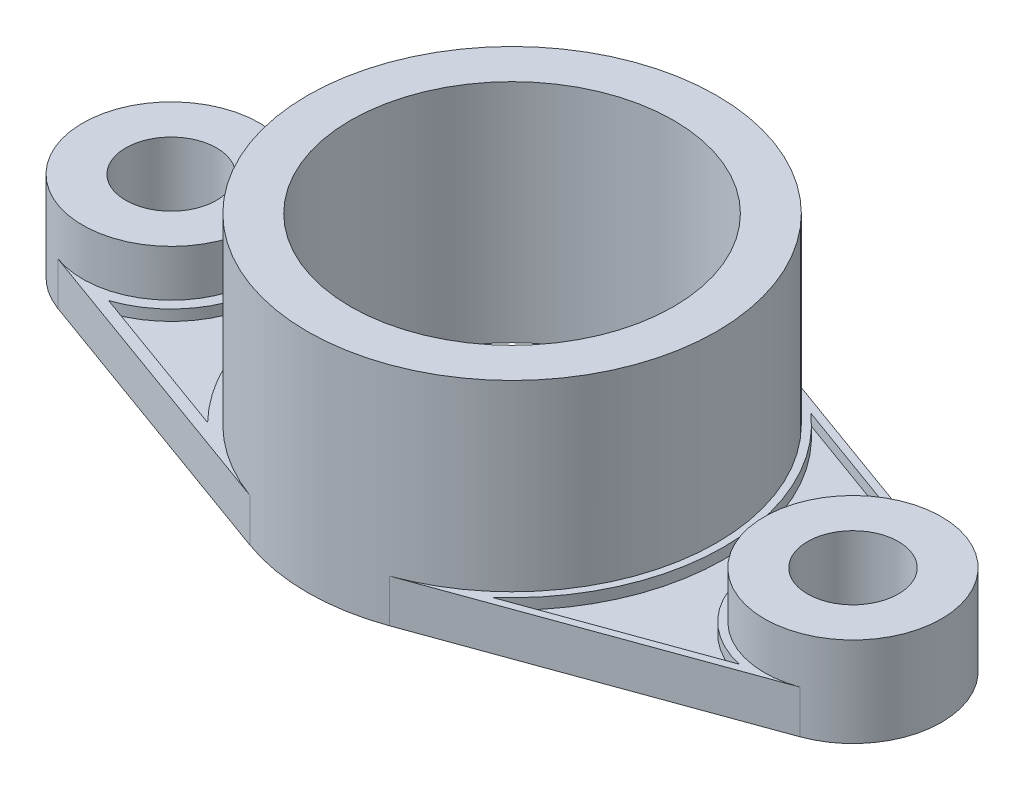
SolidWorks part; units mm, degrees
material "Polybutadiene (PB)"
ref_plane "Front Plane" through (0, 0, 0) normal (0, 0, 1) x (1, 0, 0)
ref_plane "Top Plane" through (0, 0, 0) normal (0, 1, 0) x (1, 0, 0)
ref_plane "Right Plane" through (0, 0, 0) normal (1, 0, 0) x (0, 0, -1)
sketch "Sketch1" plane through (0, 0, 0) normal (0, 1, 0) x (1, 0, 0)
  line L0 (-103.3953, 23.194) -> (-19.4, 53.597)
  line L1 (19.4, 53.597) -> (103.3953, 23.194)
  line L2 (-103.3953, -23.194) -> (-19.4, -53.597)
  line L3 (19.4, -53.597) -> (103.3953, -23.194)
  circle A0 centre (0, 0) radius 57
  circle A1 centre (0, 0) radius 45
  circle A2 centre (-95, 0) radius 12.6667
  circle A3 centre (-95, 0) radius 24.6667
  circle A4 centre (95, 0) radius 12.6667
  circle A5 centre (95, 0) radius 24.6667
  circle A6 centre (95, 0) radius 12.6667
  circle A7 centre (95, 0) radius 24.6667
  dimension "D3" = 114
  dimension "D5" = 25.3333
  dimension "D1" = 190
  dimension "D2" = 95
  dimension "D4" = 12
  dimension "D6" = 12
extrude "Boss-Extrude1" add sketch "Sketch1" along normal blind 12 contours A3 A2 | A5 A4 | A5 L1 A0 L3 | A3 L2 A0 L0 | A0 A1
sketch "Sketch2" plane through (0, 12, 0) normal (0, 1, 0) x (1, 0, 0)
  circle A0 centre (0, 0) radius 57
  circle A1 centre (0, 0) radius 45
  dimension "D1" = 114
  dimension "D2" = 12
extrude "Boss-Extrude2" add sketch "Sketch2" along normal blind 51
sketch "Sketch3" plane through (0, 12, 0) normal (0, 1, 0) x (1, 0, 0)
  line L0 (0, -34.65) -> (0, 34.65) construction
  circle A0 centre (95, 0) radius 12.6667
  circle A1 centre (95, 0) radius 24.6667
  circle A2 centre (-95, 0) radius 12.6667
  circle A3 centre (-95, 0) radius 24.6667
  dimension "D2" = 12
  dimension "D1" = 25.3333
extrude "Boss-Extrude3" add sketch "Sketch3" along normal blind 13
sketch "Sketch4" plane through (0, 12, 0) normal (0, 1, 0) x (1, 0, 0)
  line L4 (-42.9709, 41.8748) -> (-86.1968, 26.2288)
  line L5 (-86.1968, -26.2288) -> (-42.9709, -41.8748)
  line L6 (-42.9709, 41.8748) -> (-86.1968, 26.2288)
  line L7 (-86.1968, -26.2288) -> (-42.9709, -41.8748)
  line L10 (38.7986, -44.4485) -> (89.5057, -26.0945)
  line L11 (89.5057, 26.0945) -> (38.7986, 44.4485)
  line L12 (38.7986, -44.4485) -> (89.5057, -26.0945)
  line L13 (89.5057, 26.0945) -> (38.7986, 44.4485)
  arc A4 (-86.1968, -26.2288) -> (-86.1968, 26.2288) centre (-95, 0) ccw
  arc A5 (-42.9709, 41.8748) -> (-42.9709, -41.8748) centre (0, 0) ccw
  arc A6 (-86.1968, -26.2288) -> (-86.1968, 26.2288) centre (-95, 0) ccw
  arc A7 (-42.9709, 41.8748) -> (-42.9709, -41.8748) centre (0, 0) ccw
  arc A10 (89.5057, 26.0945) -> (89.5057, -26.0945) centre (95, 0) ccw
  arc A11 (38.7986, -44.4485) -> (38.7986, 44.4485) centre (0, 0) ccw
  arc A12 (89.5057, 26.0945) -> (89.5057, -26.0945) centre (95, 0) ccw
  arc A13 (38.7986, -44.4485) -> (38.7986, 44.4485) centre (0, 0) ccw
  dimension "D1" = 3
  dimension "D2" = 2
extrude "Cut-Extrude1" cut sketch "Sketch4" against normal blind 3
equation "\"A\" = 38"
equation "\"B\" = 12"
equation "\"C\"= 3"
equation "\"D1@Sketch1\"=\"A\"*5"
equation "\"D2@Sketch1\"=\"A\"*2.5"
equation "\"D3@Sketch1\"=\"A\"*3"
equation "\"D4@Sketch1\"=\"B\""
equation "\"D5@Sketch1\"=\"A\"*(2/3)"
equation "\"D6@Sketch1\"=\"B\""
equation "\"D1@Sketch2\"=\"A\"*3"
equation "\"D2@Sketch2\"=\"B\""
equation "\"D1@Sketch3\"=\"A\"*(2/3)"
equation "\"D2@Sketch3\"=\"B\""
equation "\"D1@Boss-Extrude1\"=\"C\"+9"
equation "\"D1@Boss-Extrude2\"=25-9-\"C\"+38"
equation "\"D1@Boss-Extrude3\"=-\"C\"+25-9"
equation "\"D1@Cut-Extrude1\"=\"C\""
equation "\"D1@Sketch4\"= \"C\""
